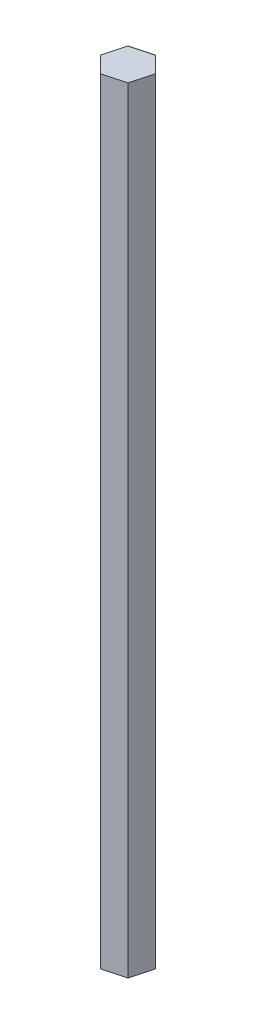
SolidWorks part; units mm, degrees
ref_plane "Front Plane" through (0, 0, 0) normal (0, 0, 1) x (1, 0, 0)
ref_plane "Top Plane" through (0, 0, 0) normal (0, 1, 0) x (1, 0, 0)
ref_plane "Right Plane" through (0, 0, 0) normal (1, 0, 0) x (0, 0, -1)
sketch "Sketch1" plane through (0, 0, 0) normal (0, 1, 0) x (1, 0, 0)
  line L1 (5.2085, -5.2085) -> (7.115, 1.9065)
  line L2 (7.115, 1.9065) -> (1.9065, 7.115)
  line L3 (1.9065, 7.115) -> (-5.2085, 5.2085)
  line L4 (-5.2085, 5.2085) -> (-7.115, -1.9065)
  line L5 (-7.115, -1.9065) -> (-1.9065, -7.115)
  line L6 (-1.9065, -7.115) -> (5.2085, -5.2085)
  circle A0 centre (0, 0) radius 6.3791 construction
extrude "Boss-Extrude1" add sketch "Sketch1" along normal blind 252.476
